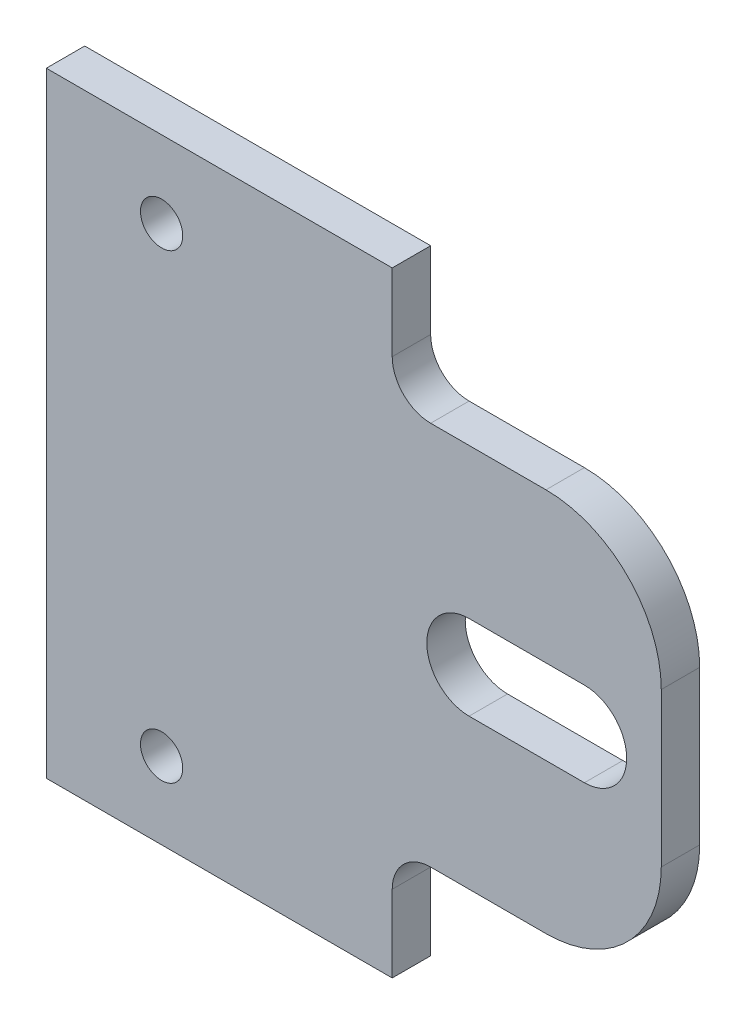
SolidWorks part; units mm, degrees
ref_plane "Plan de face" through (0, 0, 0) normal (0, 0, 1) x (1, 0, 0)
ref_plane "Plan de dessus" through (0, 0, 0) normal (0, 1, 0) x (1, 0, 0)
ref_plane "Plan de droite" through (0, 0, 0) normal (1, 0, 0) x (0, 0, -1)
sketch "Esquisse1" plane through (0, 0, 0) normal (0, 0, 1) x (1, 0, 0)
  line L0 (70, 40) -> (55, 40) construction
  line L1 (0, 0) -> (80, 0)
  line L2 (0, 0) -> (0, 80)
  line L3 (0, 80) -> (80, 80)
  line L4 (80, 0) -> (80, 80)
  line L5 (80, 80) -> (45, 80)
  line L6 (80, 80) -> (80, 65)
  line L7 (80, 65) -> (45, 65)
  line L8 (45, 80) -> (45, 65)
  line L9 (80, 0) -> (45, 0)
  line L10 (80, 0) -> (80, 15)
  line L11 (80, 15) -> (45, 15)
  line L12 (45, 0) -> (45, 15)
  line L13 (70, 34.5) -> (55, 34.5)
  line L14 (70, 45.5) -> (55, 45.5)
  circle A0 centre (15, 70) radius 2.75
  circle A1 centre (15, 10) radius 2.75
  arc A2 (70, 34.5) -> (70, 45.5) centre (70, 40) ccw
  arc A3 (55, 45.5) -> (55, 34.5) centre (55, 40) ccw
  point P17 (62.5, 40)
  dimension "D7" = 10
  dimension "D8" = 10
  dimension "D9" = 15
  dimension "D10" = 15
  dimension "D11" = 5.5
  dimension "D12" = 5.5
  dimension "D1" = 80
  dimension "D2" = 80
  dimension "D3" = 50
  dimension "D4" = 15
  dimension "D5" = 35
  dimension "D6" = 35
  dimension "D13" = 11
  dimension "D14" = 25
  dimension "D15" = 10
  dimension "D16" = 15
extrude "Boss.-Extru.1" add sketch "Esquisse1" along normal blind 5 contours L1 L12 L11 L4 L7 L8 L3 L2 A3 L14 A2 L13 A1 A0
fillet "Congé1" radius 5 2 edges at (45, 15, 2.5) (45, 65, 2.5)
fillet "Congé2" radius 15 2 edges at (80, 15, 2.5) (80, 65, 2.5)
